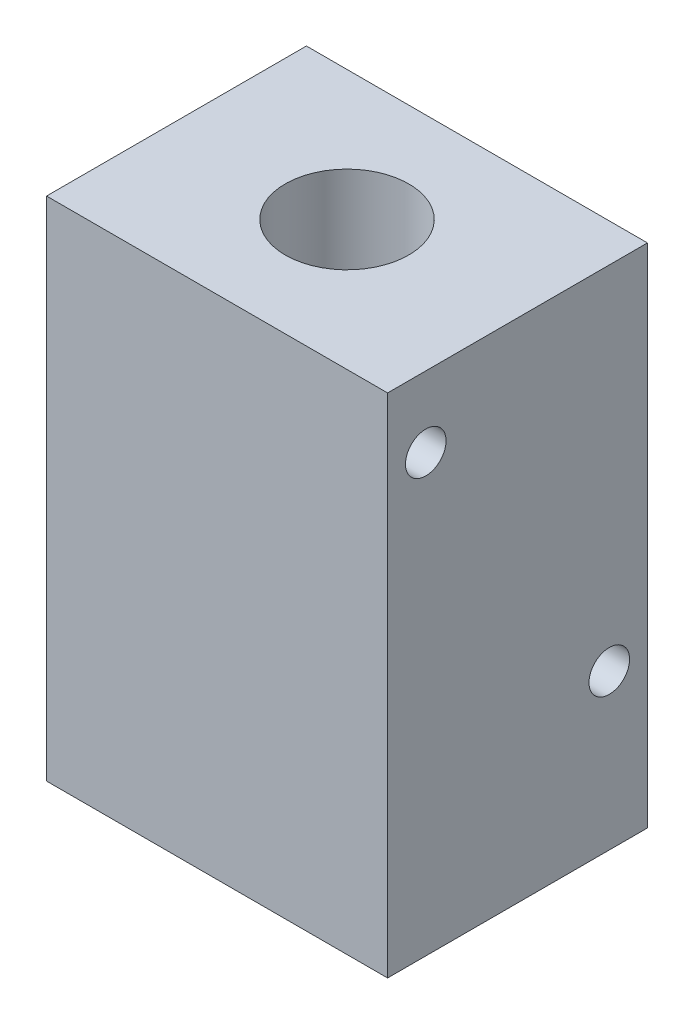
SolidWorks part; units mm, degrees
ref_plane "Front Plane" through (0, 0, 0) normal (0, 0, 1) x (1, 0, 0)
ref_plane "Top Plane" through (0, 0, 0) normal (0, 1, 0) x (1, 0, 0)
ref_plane "Right Plane" through (0, 0, 0) normal (1, 0, 0) x (0, 0, -1)
sketch "Sketch1" plane through (0, 0, 0) normal (0, 1, 0) x (1, 0, 0)
  line L1 (0, 0) -> (26.67, 0)
  line L2 (0, 0) -> (0, 20.32)
  line L3 (0, 20.32) -> (26.67, 20.32)
  line L4 (26.67, 0) -> (26.67, 20.32)
  dimension "D1" = 26.67
  dimension "D2" = 20.32
extrude "Boss-Extrude1" add sketch "Sketch1" along normal blind 39.624
sketch "Sketch2" plane through (0, 0, 0) normal (0, -1, 0) x (1, 0, 0)
  line L0 (13.335, 0) -> (13.335, -20.32) construction
  line L1 (0, 0) -> (26.67, 0) construction
  line L2 (26.67, -20.32) -> (0, -20.32) construction
  line L3 (0, -10.16) -> (26.67, -10.16) construction
  line L4 (0, -20.32) -> (0, 0) construction
  line L5 (26.67, 0) -> (26.67, -20.32) construction
  circle A0 centre (13.335, -10.16) radius 2.413
  point P14 (13.335, -10.16)
  dimension "D1" = 4.826
extrude "Cut-Extrude1" cut sketch "Sketch2" against normal through all
sketch "Sketch3" plane through (0, 39.624, 0) normal (0, 1, 0) x (1, 0, 0)
  circle A1 centre (13.335, 10.16) radius 4.826
  dimension "D1" = 9.652
extrude "Cut-Extrude2" cut sketch "Sketch3" against normal blind 28.448
sketch "Sketch4" plane through (26.67, 0, 0) normal (1, 0, 0) x (0, 0, -1)
  line L0 (0, 39.624) -> (20.32, 39.624) construction
  line L1 (0, 39.624) -> (0, 0) construction
  line L2 (20.32, 39.624) -> (20.32, 0) construction
  circle A0 centre (2.9845, 34.0995) radius 1.5875
  circle A1 centre (17.3355, 12.1285) radius 1.5875
  point P4 (2.9845, 35.687)
  point P5 (1.397, 34.0995)
  point P6 (18.923, 12.1285)
  point P7 (17.3355, 10.541)
  point P8 (17.3355, 13.716)
  dimension "D1" = 3.175
  dimension "D2" = 3.937
  dimension "D3" = 1.397
  dimension "D4" = 25.908
  dimension "D5" = 1.397
extrude "Cut-Extrude3" cut sketch "Sketch4" against normal blind 2.54
